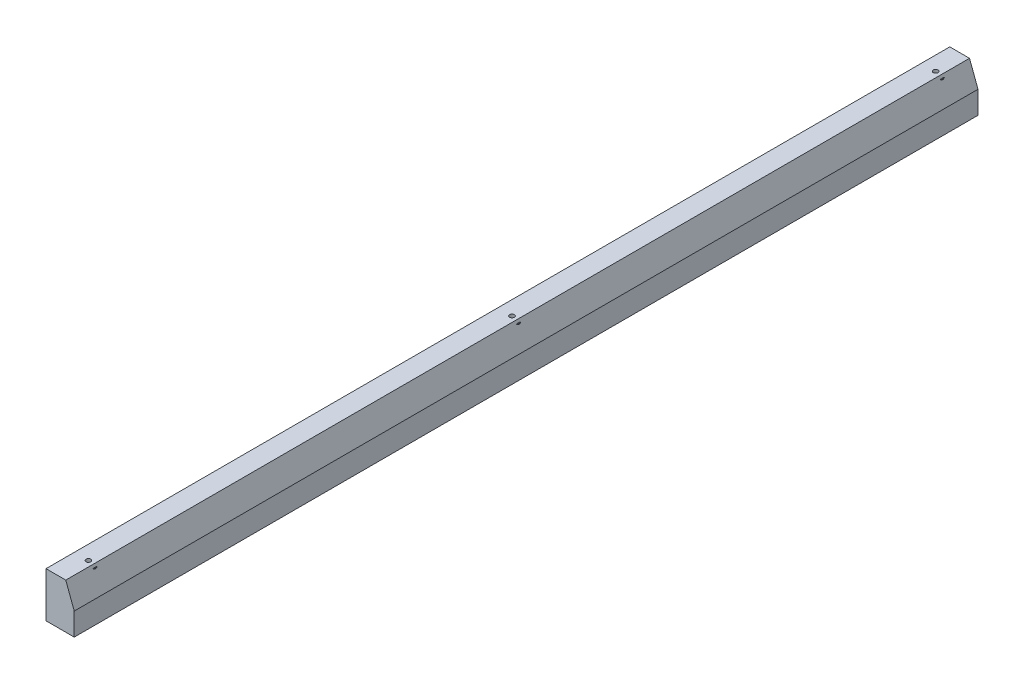
SolidWorks part; units mm, degrees
material "A3钢"
ref_plane "前视基准面" through (0, 0, 0) normal (0, 0, 1) x (1, 0, 0)
ref_plane "上视基准面" through (0, 0, 0) normal (0, 1, 0) x (1, 0, 0)
ref_plane "右视基准面" through (0, 0, 0) normal (1, 0, 0) x (0, 0, -1)
sketch "草图1" plane through (0, 0, 0) normal (0, 0, 1) x (1, 0, 0)
  line L0 (-58.1749, 0) -> (53.5621, 0) construction
  line L1 (0, 19.1787) -> (0, -27.9938) construction
  line L2 (0, 0) -> (10, 0)
  line L3 (10, 0) -> (10, 16)
  line L4 (10, 16) -> (0, 16)
  line L5 (0, 16) -> (0, 0)
  dimension "D3" = 16
  dimension "D4" = 10
extrude "凸台-拉伸1" add sketch "草图1" along normal blind 320
sketch "草图3" plane through (0, 0, 0) normal (-1, 0, 0) x (0, 0, 1)
  line L0 (320, 0) -> (320, 16) construction
  line L3 (320, 16) -> (0, 16) construction
  line L4 (30, 8.5) -> (290, 8.5)
  line L5 (30, 8.5) -> (30, -6.5)
  line L6 (30, -6.5) -> (290, -6.5)
  line L7 (290, 8.5) -> (290, -6.5)
  line L8 (30, 8.5) -> (290, -6.5) construction
  line L9 (30, -6.5) -> (290, 8.5) construction
  dimension "D3" = 30
  dimension "D4" = 7.5
  dimension "D1" = 260
  dimension "D2" = 15
sketch "草图7" plane through (10, 0, 0) normal (0, 1, 0) x (0, 0, -1)
  line L0 (-160, 0) -> (-160, -23.9428) construction
  line L1 (-320, 0) -> (0, 0) construction
  line L2 (-310, 5) -> (-160, 5) construction
  line L3 (-160, 5) -> (-10, 5) construction
  line L4 (-320, 0) -> (0, 0) construction
  dimension "D1" = 5
  dimension "D2" = 150
  dimension "D3" = 150
hole_wizard "M6 螺纹孔1" positions "3D草图1" profile "草图9" tap size "M6" standard "GB"
sketch3d "3D草图1"
  point P0 (5, 0, 310)
  point P3 (5, 0, 160)
  point P6 (5, 0, 10)
sketch "草图9" plane through (5, 0, 310) normal (1, 0, 0) x (0, 0, -1)
  line L0 (0, 0) -> (0, 16.5022)
  line L1 (0, 16.5022) -> (2.5, 15)
  line L2 (2.5, 15) -> (2.5, 0)
  line L5 (2.5, 0) -> (0, 0)
  line L10 (0, 16.5022) -> (-2.5, 15) construction
  line L11 (0, -6.35) -> (0, 107.95) construction
  dimension "螺纹孔钻头直径" = 5
  dimension "螺纹孔钻头深度" = 15
  dimension "导头角度" = 118
cosmetic thread "孔螺蚊线1" parameters "D1"=12, "D2"=6
cosmetic thread "孔螺蚊线2" parameters "D1"=12, "D2"=6
cosmetic thread "孔螺蚊线3" parameters "D1"=12, "D2"=6
chamfer "倒角1" distance 8 distance2 3 1 edges at (10, 16, 160)
